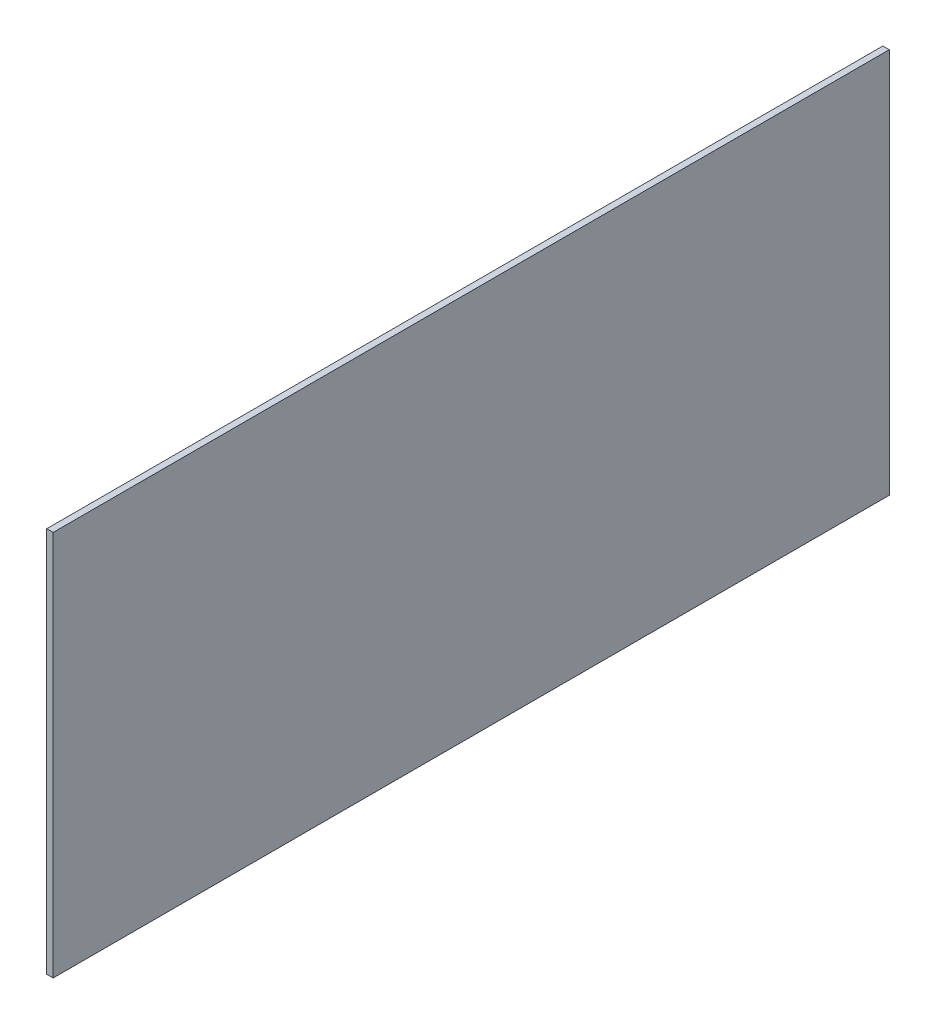
SolidWorks part; units mm, degrees
ref_plane "Front Plane" through (0, 0, 0) normal (0, 0, 1) x (1, 0, 0)
ref_plane "Top Plane" through (0, 0, 0) normal (0, 1, 0) x (1, 0, 0)
ref_plane "Right Plane" through (0, 0, 0) normal (1, 0, 0) x (0, 0, -1)
sketch "Sketch1" plane through (0, 0, 0) normal (1, 0, 0) x (0, 0, -1)
  line L1 (-33.8535, 9.9811) -> (96.1465, 9.9811)
  line L2 (-33.8535, 9.9811) -> (-33.8535, -50.0189)
  line L3 (-33.8535, -50.0189) -> (96.1465, -50.0189)
  line L4 (96.1465, 9.9811) -> (96.1465, -50.0189)
  dimension "D1" = 130
  dimension "D2" = 60
extrude "Boss-Extrude1" add sketch "Sketch1" along normal blind 1
